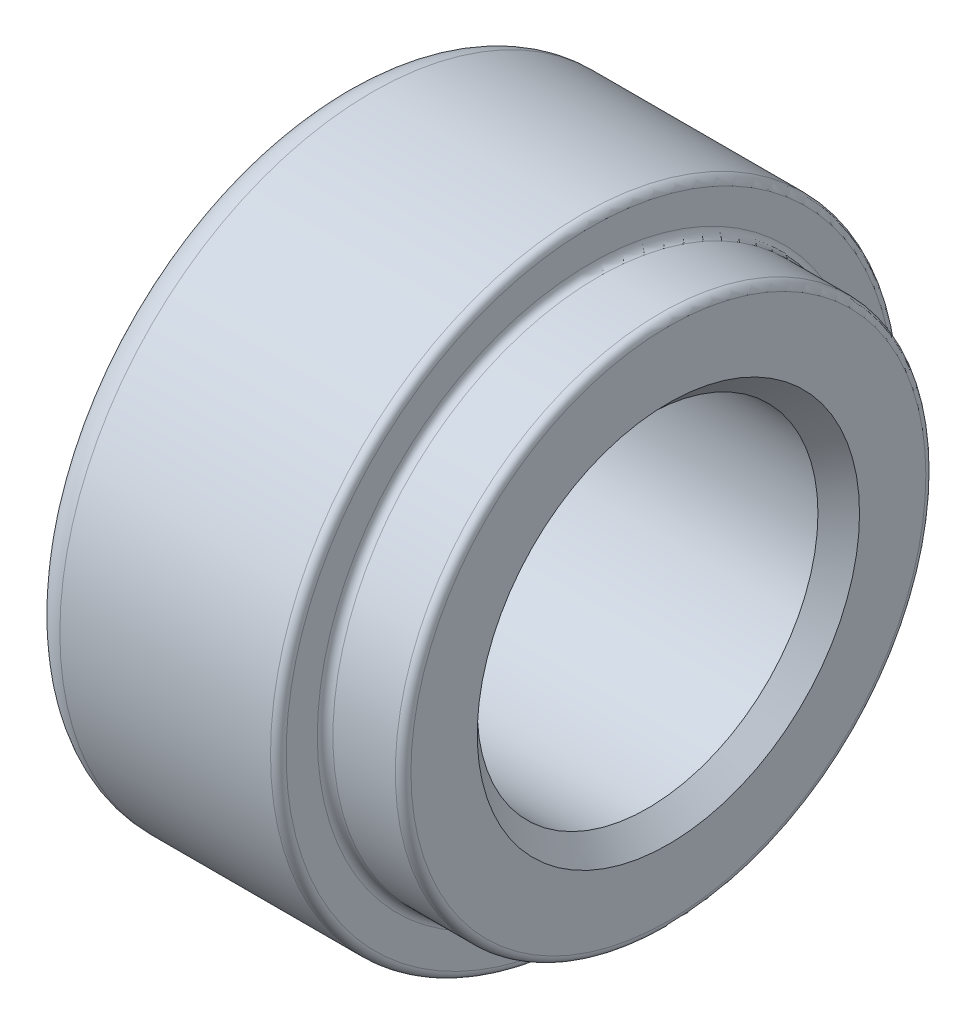
SolidWorks part; units mm, degrees
ref_plane "Plane1" through (0, 0, 0) normal (0, 0, 1) x (1, 0, 0)
ref_plane "Plane2" through (0, 0, 0) normal (0, 1, 0) x (1, 0, 0)
ref_plane "Plane3" through (0, 0, 0) normal (1, 0, 0) x (0, 0, -1)
sketch "Sketch1" plane through (0, 0, 0) normal (0, 0, 1) x (1, 0, 0)
  line L0 (0, 12.25) -> (0, 16.5)
  line L1 (-0.5, 17) -> (-4.5, 17)
  line L2 (-21, 18) -> (-21, 12.25)
  line L3 (-21, 12.25) -> (-19.6675, 10.9175)
  line L4 (-1.3325, 10.9175) -> (0, 12.25)
  line L5 (-5, 17.5) -> (-5, 19.5)
  line L6 (-5.5, 20) -> (-19, 20)
  line L12 (-19.6675, 10.9175) -> (-1.3325, 10.9175)
  line L13 (0, 0) -> (-20, 0) construction
  arc A0 (-19, 20) -> (-21, 18) centre (-19, 18) ccw
  arc A1 (-4.5, 17) -> (-5, 17.5) centre (-4.5, 17.5) cw
  arc A2 (-5.5, 20) -> (-5, 19.5) centre (-5.5, 19.5) cw
  arc A3 (-0.5, 17) -> (0, 16.5) centre (-0.5, 16.5) cw
  point P0 (0, 10.9175)
  point P12 (-21, 10.9175)
  dimension "D5" = 2
  dimension "D11" = 0.5
  dimension "D2" = 45
  dimension "D3" = 34
  dimension "D4" = 21.835
  dimension "D6" = 24.5
  dimension "D7" = 45
  dimension "D8" = 21
  dimension "D9" = 5
  dimension "D10" = 40
  dimension "D12" = 24.5
revolve "Base-Revolve" add sketch "Sketch1" angle 360 about L13
cosmetic thread "Cosmetic Thread1" parameters "D2"=24
